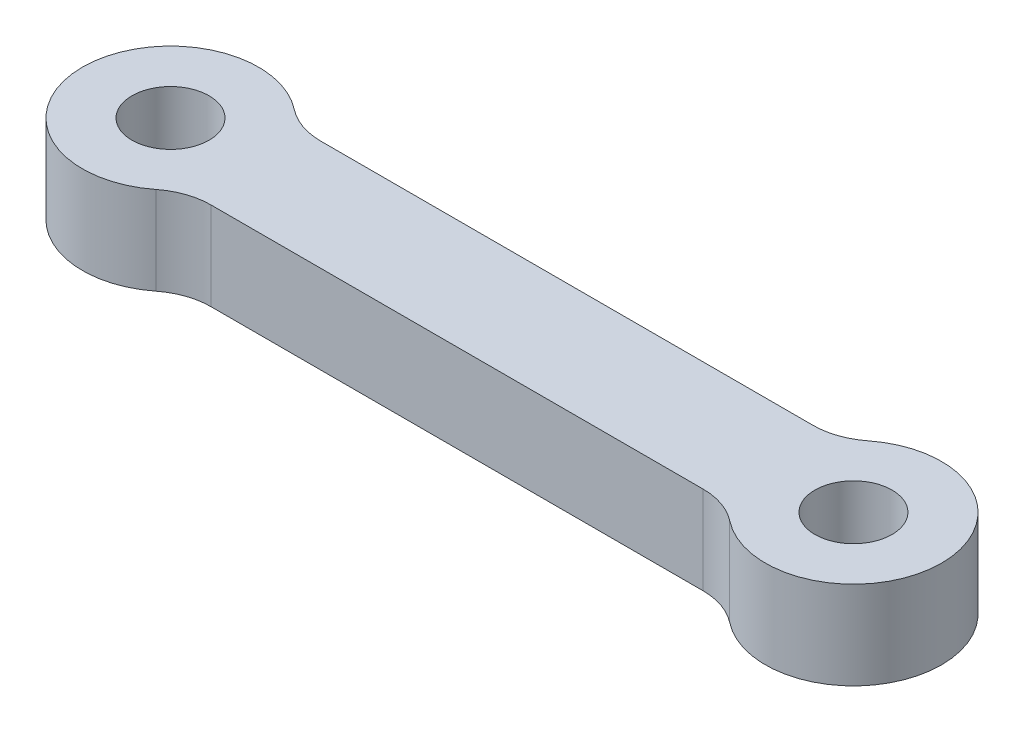
SolidWorks part; units mm, degrees
ref_plane "Front Plane" through (0, 0, 0) normal (0, 0, 1) x (1, 0, 0)
ref_plane "Top Plane" through (0, 0, 0) normal (0, 1, 0) x (1, 0, 0)
ref_plane "Right Plane" through (0, 0, 0) normal (1, 0, 0) x (0, 0, -1)
sketch "Sketch1" plane through (0, 0, 0) normal (0, 1, 0) x (1, 0, 0)
  line L0 (0, 0) -> (31000, 0) construction
  line L1 (3122.499, 2500) -> (27877.501, 2500)
  line L2 (3122.499, -2500) -> (27877.501, -2500)
  circle A0 centre (0, 0) radius 1750
  circle A1 centre (0, 0) radius 4000
  circle A2 centre (31000, 0) radius 1750
  circle A3 centre (31000, 0) radius 4000
  dimension "D2" = 3500
  dimension "D3" = 8000
  dimension "D1" = 31000
  dimension "D4" = 5000
extrude "Boss-Extrude1" add sketch "Sketch1" along normal blind 4000
fillet "Fillet1" radius 3000 4 edges at (3122.499, 2000, -2500) (3122.499, 2000, 2500) (27877.501, 2000, -2500) (27877.501, 2000, 2500)
